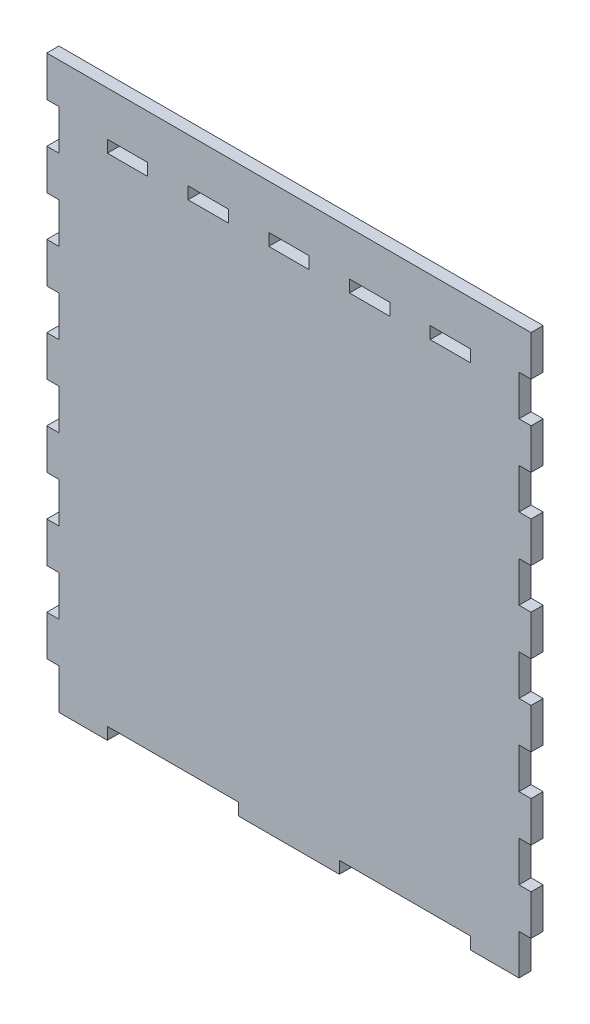
SolidWorks part; units mm, degrees
ref_plane "Front Plane" through (0, 0, 0) normal (0, 0, 1) x (1, 0, 0)
ref_plane "Top Plane" through (0, 0, 0) normal (0, 1, 0) x (1, 0, 0)
ref_plane "Right Plane" through (0, 0, 0) normal (1, 0, 0) x (0, 0, -1)
sketch "Sketch1" plane through (0, 0, 0) normal (0, 0, 1) x (1, 0, 0)
  line L1 (-120, 140) -> (120, 140)
  line L2 (-120, 140) -> (-120, -140)
  line L3 (-120, -140) -> (120, -140)
  line L4 (120, 140) -> (120, -140)
  dimension "D1" = 120
  dimension "D2" = 140
  dimension "D3" = 280
  dimension "D4" = 240
extrude "Boss-Extrude1" add sketch "Sketch1" against normal blind 6
sketch "Sketch3" plane through (0, 0, 0) normal (0, 0, 1) x (1, 0, 0)
  line L0 (120, -140) -> (120, 140) construction
  line L1 (120, 120) -> (114, 120)
  line L2 (120, 120) -> (120, 100)
  line L3 (120, 100) -> (114, 100)
  line L4 (114, 120) -> (114, 100)
  line L5 (120, 140) -> (-120, 140) construction
  line L6 (0, 185.2993) -> (0, -160.0565) construction
  line L7 (120, 80) -> (114, 80)
  line L8 (120, 80) -> (120, 60)
  line L9 (120, 60) -> (114, 60)
  line L10 (114, 80) -> (114, 60)
  line L11 (120, 40) -> (114, 40)
  line L12 (120, 40) -> (120, 20)
  line L13 (120, 20) -> (114, 20)
  line L14 (114, 40) -> (114, 20)
  line L15 (120, 0) -> (114, 0)
  line L16 (120, 0) -> (120, -20)
  line L17 (120, -20) -> (114, -20)
  line L18 (114, 0) -> (114, -20)
  line L19 (120, -40) -> (114, -40)
  line L20 (-120, 120) -> (-120, 100)
  line L21 (120, -40) -> (120, -60)
  line L22 (120, -60) -> (114, -60)
  line L23 (114, -40) -> (114, -60)
  line L24 (-120, 120) -> (-114, 120)
  line L25 (-114, 120) -> (-114, 100)
  line L26 (-120, 100) -> (-114, 100)
  line L27 (-120, 80) -> (-120, 60)
  line L28 (-120, 80) -> (-114, 80)
  line L29 (-114, 80) -> (-114, 60)
  line L30 (-120, 60) -> (-114, 60)
  line L31 (-120, 40) -> (-114, 40)
  line L32 (-114, 40) -> (-114, 20)
  line L33 (-120, 40) -> (-120, 20)
  line L34 (-120, 20) -> (-114, 20)
  line L35 (-120, 0) -> (-114, 0)
  line L36 (-114, 0) -> (-114, -20)
  line L37 (-120, 0) -> (-120, -20)
  line L38 (-120, -20) -> (-114, -20)
  line L39 (-120, -40) -> (-114, -40)
  line L40 (-114, -40) -> (-114, -60)
  line L41 (-120, -40) -> (-120, -60)
  line L42 (-120, -60) -> (-114, -60)
  line L43 (120, -140) -> (120, 140) construction
  line L44 (120, -80) -> (114, -80)
  line L45 (120, -80) -> (120, -100)
  line L46 (120, -100) -> (114, -100)
  line L47 (114, -80) -> (114, -100)
  line L48 (-114, -80) -> (-114, -100)
  line L49 (-120, -100) -> (-114, -100)
  line L50 (-120, -80) -> (-120, -100)
  line L51 (-120, -80) -> (-114, -80)
  dimension "D1" = 20
  dimension "D2" = 6
  dimension "D3" = 20
  dimension "D4" = 20
  dimension "D5" = 20
  dimension "D6" = 20
  dimension "D7" = 20
  dimension "D8" = 20
  dimension "D9" = 20
  dimension "D10" = 20
  dimension "D11" = 20
  dimension "D12" = 6
  dimension "D13" = 6
  dimension "D14" = 6
  dimension "D15" = 6
  dimension "D16" = 20
  dimension "D17" = 20
extrude "Cut-Extrude1" cut sketch "Sketch3" against normal blind 6
sketch "Sketch4" plane through (0, 0, 0) normal (0, 0, 1) x (1, 0, 0)
  line L1 (120, -140) -> (120, -100) construction
  line L2 (120, -120) -> (114, -120)
  line L3 (120, -120) -> (120, -140)
  line L4 (120, -140) -> (114, -140)
  line L5 (114, -120) -> (114, -140)
  line L6 (-120, -140) -> (120, -140) construction
  line L7 (0, 211.6851) -> (0, -211.5209) construction
  line L8 (90, -140) -> (25, -140)
  line L9 (90, -140) -> (90, -134)
  line L10 (90, -134) -> (25, -134)
  line L11 (25, -140) -> (25, -134)
  line L12 (-25, -140) -> (-25, -134)
  line L13 (-90, -140) -> (-90, -134)
  line L14 (-90, -140) -> (-25, -140)
  line L15 (-90, -134) -> (-25, -134)
  line L16 (-120, -140) -> (-114, -140)
  line L17 (-120, -120) -> (-120, -140)
  line L18 (-114, -120) -> (-114, -140)
  line L19 (-120, -120) -> (-114, -120)
  point P23 (0, 0)
  point P24 (0, 0)
  dimension "D1" = 6
  dimension "D2" = 20
  dimension "D3" = 65
  dimension "D4" = 30
  dimension "D5" = 6
extrude "Cut-Extrude2" cut sketch "Sketch4" against normal blind 6
sketch "Sketch5" plane through (0, 0, 0) normal (0, 0, 1) x (1, 0, 0)
  line L0 (0, 0) -> (0, 153.5835) construction
  line L1 (-10, 118) -> (10, 118)
  line L2 (-90, 118) -> (-90, 112)
  line L3 (-10, 112) -> (10, 112)
  line L4 (10, 118) -> (10, 112)
  line L5 (30, 118) -> (50, 118)
  line L6 (30, 118) -> (30, 112)
  line L7 (30, 112) -> (50, 112)
  line L8 (50, 118) -> (50, 112)
  line L9 (70, 118) -> (90, 118)
  line L10 (70, 118) -> (70, 112)
  line L11 (70, 112) -> (90, 112)
  line L12 (90, 118) -> (90, 112)
  line L13 (-70, 112) -> (-90, 112)
  line L14 (-70, 118) -> (-90, 118)
  line L15 (-70, 118) -> (-70, 112)
  line L16 (-50, 118) -> (-50, 112)
  line L17 (-30, 112) -> (-50, 112)
  line L18 (-30, 118) -> (-50, 118)
  line L19 (-30, 118) -> (-30, 112)
  line L20 (-10, 118) -> (-10, 112)
  point P13 (10, 115)
  point P25 (0, 112)
  point P26 (0, 118)
  dimension "D1" = 112
  dimension "D2" = 6
  dimension "D3" = 10
  dimension "D5" = 20
  dimension "D6" = 20
  dimension "D7" = 20
  dimension "D8" = 20
  dimension "D9" = 6
  dimension "D10" = 6
  dimension "D11" = 112
  dimension "D12" = 112
extrude "Cut-Extrude3" cut sketch "Sketch5" against normal blind 6
equation "\"Material Thickness\"= 6"
